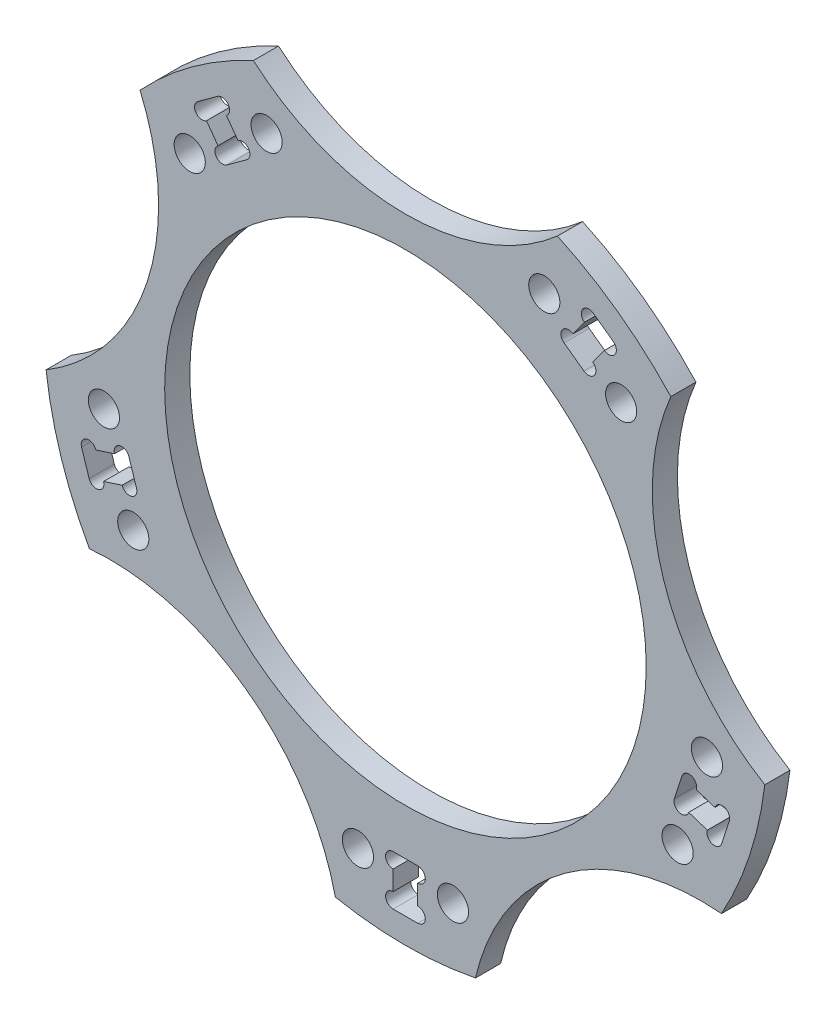
SolidWorks part; units mm, degrees
ref_plane "前视基准面" through (0, 0, 0) normal (0, 0, 1) x (1, 0, 0)
ref_plane "上视基准面" through (0, 0, 0) normal (0, 1, 0) x (1, 0, 0)
ref_plane "右视基准面" through (0, 0, 0) normal (1, 0, 0) x (0, 0, -1)
sketch "草图1" plane through (0, 0, 0) normal (0, 0, 1) x (1, 0, 0)
  arc A0 (-15.1219, 32.67) -> (-26.3981, 24.4773) centre (0, 0) ccw
  circle A1 centre (0, 0) radius 23.95
  arc A2 (-15.1219, 32.67) -> (15.1219, 32.67) centre (0, 50) ccw
  arc A3 (26.3981, 24.4773) -> (35.7439, -4.2862) centre (47.5528, 15.4508) ccw
  arc A4 (31.4368, -17.5422) -> (6.9691, -35.319) centre (29.3893, -40.4508) ccw
  arc A5 (-6.9691, -35.319) -> (-31.4368, -17.5422) centre (-29.3893, -40.4508) ccw
  arc A6 (-35.7439, -4.2862) -> (-26.3981, 24.4773) centre (-47.5528, 15.4508) ccw
  arc A7 (26.3981, 24.4773) -> (15.1219, 32.67) centre (0, 0) ccw
  arc A8 (31.4368, -17.5422) -> (35.7439, -4.2862) centre (0, 0) ccw
  arc A9 (-6.9691, -35.319) -> (6.9691, -35.319) centre (0, 0) ccw
  arc A10 (-35.7439, -4.2862) -> (-31.4368, -17.5422) centre (0, 0) ccw
  point P21 (0, 0)
  dimension "D1" = 50
  dimension "D2" = 46
  dimension "D3" = 47.9
  dimension "D4" = 36
  dimension "D5" = 5
extrude "凸台-拉伸1" add sketch "草图1" along normal mid plane 2.5
sketch "草图2" plane through (0, 0, 1.25) normal (0, 0, 1) x (1, 0, 0)
  line L1 (1.225, -33.475) -> (-1.225, -33.475)
  line L2 (1.225, -33.475) -> (1.225, -28.525)
  line L3 (1.225, -28.525) -> (-1.225, -28.525)
  line L4 (-1.225, -33.475) -> (-1.225, -28.525)
  line L5 (1.225, -33.475) -> (-1.225, -28.525) construction
  line L6 (1.225, -28.525) -> (-1.225, -33.475) construction
  circle A0 centre (0, 0) radius 31 construction
  point P0 (0, -31)
  dimension "D1" = 62
  dimension "D2" = 2.45
  dimension "D3" = 4.95
extrude "切除-拉伸1" cut sketch "草图2" against normal through all
sketch "草图3" plane through (0, 0, 1.25) normal (0, 0, 1) x (1, 0, 0)
  line L0 (-1.225, -28.525) -> (-1.225, -33.475) construction
  line L1 (1.225, -33.475) -> (1.225, -28.525) construction
  circle A0 centre (-1.225, -29.275) radius 0.75
  circle A1 centre (1.225, -29.275) radius 0.75
  circle A2 centre (-1.225, -32.725) radius 0.75
  circle A3 centre (1.225, -32.725) radius 0.75
  dimension "D1" = 1.5
extrude "切除-拉伸2" cut sketch "草图3" against normal through all
sketch "草图4" plane through (0, 0, 1.25) normal (0, 0, 1) x (1, 0, 0)
  line L0 (-1.225, -30.025) -> (-1.225, -31.975) construction
  line L1 (0, -28.525) -> (0, -33.475) construction
  line L2 (1.225, -28.525) -> (-1.225, -28.525) construction
  line L3 (-1.225, -33.475) -> (1.225, -33.475) construction
  circle A0 centre (-4.725, -30) radius 3.5 construction
  circle A1 centre (-4.725, -30) radius 1.55
  circle A2 centre (4.725, -30) radius 1.55
  arc A3 (-6.9691, -35.319) -> (6.9691, -35.319) centre (0, 0) ccw construction
  point P17 (0, -36)
  dimension "D1" = 7
  dimension "D2" = 3.1
  dimension "D3" = 6
extrude "切除-拉伸3" cut sketch "草图4" against normal through all
pattern_circular "阵列(圆周)1" count 5 over 360 about axis through (0, 0, 0) along (0, 0, 1) of "切除-拉伸1", "切除-拉伸2", "切除-拉伸3"
